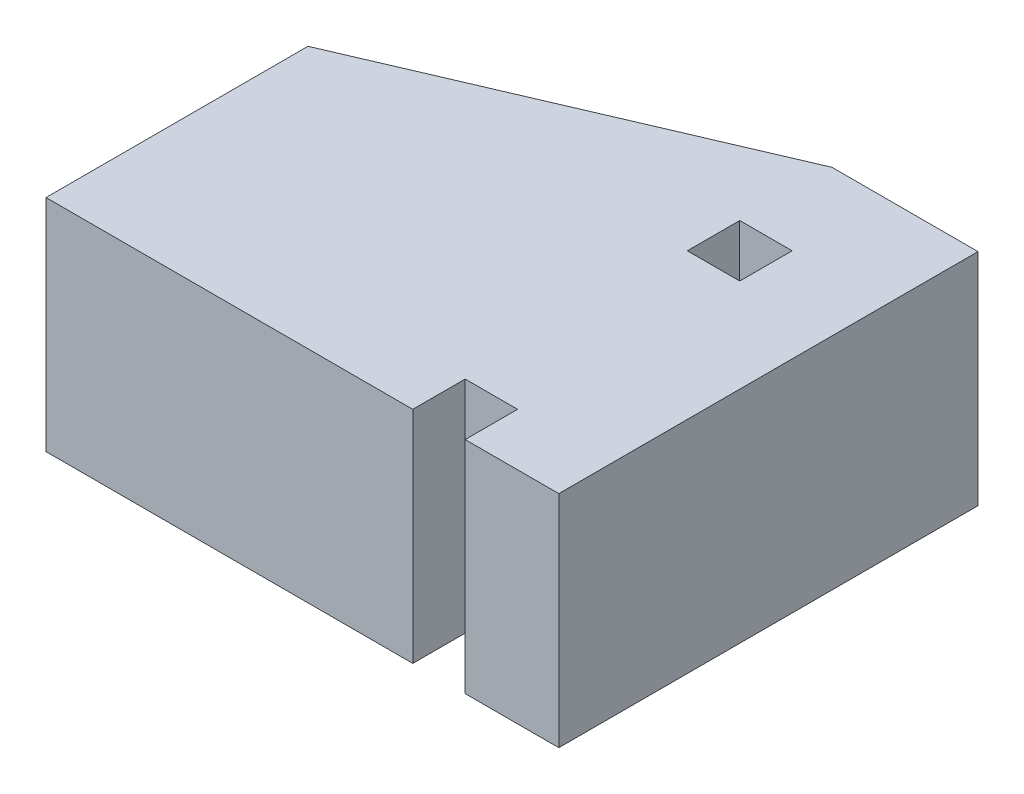
SolidWorks part; units mm, degrees
material "Plomb pur"
ref_plane "Plan de face" through (0, 0, 0) normal (0, 0, 1) x (1, 0, 0)
ref_plane "Plan de dessus" through (0, 0, 0) normal (0, 1, 0) x (1, 0, 0)
ref_plane "Plan de droite" through (0, 0, 0) normal (1, 0, 0) x (0, 0, -1)
sketch "Esquisse1" plane through (0, 0, 0) normal (0, 1, 0) x (1, 0, 0)
  line L0 (0, -21.2) -> (0, -31.2)
  line L1 (0, -31.2) -> (17.87, -31.2)
  line L2 (17.87, -31.2) -> (17.87, 48.8)
  line L3 (0, -21.2) -> (-10, -21.2)
  line L4 (-10, -21.2) -> (-10, -31.2)
  line L5 (-10, -31.2) -> (-80, -31.2)
  line L6 (-80, -31.2) -> (-80, 18.8)
  line L7 (-80, 18.8) -> (-10, 48.8)
  line L8 (0, 0) -> (-108.9882, 0) construction
  line L9 (-10, 21.2) -> (-10, 31.2)
  line L10 (0, 21.2) -> (-10, 21.2)
  line L11 (0, 21.2) -> (0, 31.2)
  line L12 (0, 31.2) -> (-10, 31.2)
  line L13 (-10, 48.8) -> (17.87, 48.8)
  line L14 (17.87, -4) -> (17.87, 4) construction
  line L15 (0, -21.2) -> (-9, -21.2) construction
  dimension "D1" = 70
  dimension "D2" = 80
  dimension "D3" = 50
extrude "Boss.-Extru.1" add sketch "Esquisse1" along normal blind 42
sketch "Esquisse2" plane through (0, 42, 0) normal (0, 1, 0) x (1, 0, 0)
  line L0 (17.87, 31.2) -> (17.87, 71.2)
  line L1 (5.87, 71.2) -> (-42.13, 31.2)
  line L2 (-10, 48.8) -> (-80, 18.8) construction
  line L3 (-42.13, 31.2) -> (17.87, 31.2)
  line L4 (17.87, 71.2) -> (5.87, 71.2)
  dimension "D2" = 60
  dimension "D3" = 40
  dimension "D4" = 12
extrude "Boss.-Extru.2" [suppressed] add sketch "Esquisse2" against normal blind 80
sketch "Esquisse3" [suppressed] plane through (17.87, 0, 0) normal (1, 0, 0) x (0, 0, -1)
  line L0 (31.2, -38) -> (51.2, -38)
  line L1 (31.2, -38) -> (71.2, -38) construction
  line L2 (51.2, -38) -> (31.2, -18)
  line L3 (31.2, -38) -> (31.2, 0) construction
  line L4 (31.2, -18) -> (31.2, -38)
  dimension "D1" = 20
extrude "Enlèv. mat.-Extru.1" [suppressed] cut sketch "Esquisse3" against normal up to surface (17.87 mm away)
